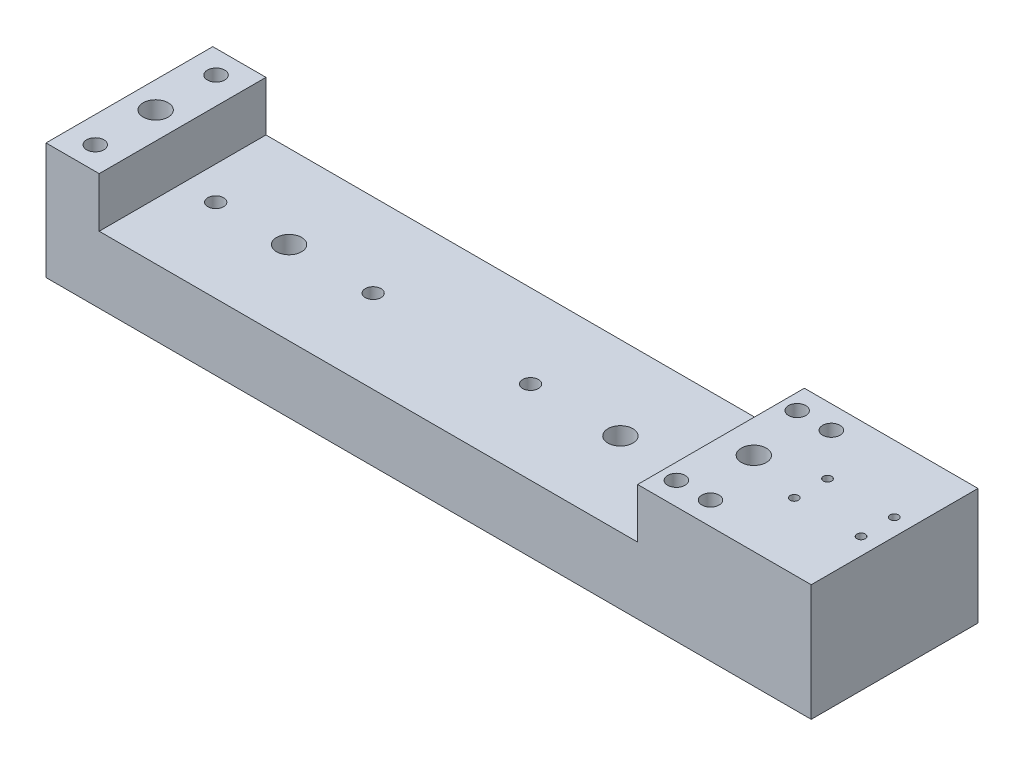
SolidWorks part; units mm, degrees
material "McMaster 6061-T6"
ref_plane "Front Plane" through (0, 0, 0) normal (0, 0, 1) x (1, 0, 0)
ref_plane "Top Plane" through (0, 0, 0) normal (0, 1, 0) x (1, 0, 0)
ref_plane "Right Plane" through (0, 0, 0) normal (1, 0, 0) x (0, 0, -1)
sketch "Sketch1" plane through (0, 0, 0) normal (0, 0, 1) x (1, 0, 0)
  line L0 (-125.125, 0) -> (-125.125, -6.35)
  line L1 (-125.125, -6.35) -> (166.225, -6.35)
  line L2 (166.225, -6.35) -> (166.225, 0)
  line B0 (-125.125, 38.05) -> (-104.875, 38.05)
  line B1 (-104.875, 38.05) -> (-104.875, 19.05)
  line B2 (-104.875, 19.05) -> (100.125, 19.05)
  line B3 (100.125, 19.05) -> (100.125, 38.05)
  line B4 (100.125, 38.05) -> (125.125, 38.05)
  line B5 (-125.125, 38.05) -> (-125.125, 0)
  line B6 (-125.125, 0) -> (125.125, 0)
  line B7 (125.125, 0) -> (125.125, 38.05)
  line B8 (125.125, 38.05) -> (166.225, 38.05)
  line B9 (166.225, 38.05) -> (166.225, 0)
  line B10 (166.225, 0) -> (125.125, 0)
  dimension "D1" = 25.4
sketch_block_instance "Block-MainBlock Sideview-1"
sketch_block "Block-MainBlock Sideview" parameters "D1"=19.05, "D2"=38.05
extrude "Main Extrude" add sketch "Sketch1" along normal blind 63.5 contours B6 B7 B4 B3 B2 B1 B0 B5 | B10 B9 B8 B7 | B6 L0 L1 L2
sketch "Sketch3" plane through (0, 38.05, 0) normal (0, 1, 0) x (1, 0, 0)
  line L0 (166.225, -63.5) -> (166.225, 0) construction
  line L1 (125.125, -31.75) -> (166.225, -31.75) construction
  line L2 (166.225, -63.5) -> (166.225, 0) construction
  point P4 (166.225, -31.75)
  line B0 (-105.125, -1.75) -> (-105.125, -61.75)
  line B1 (-105.125, -1.75) -> (-125.125, -1.75)
  line B2 (-125.125, -1.75) -> (-125.125, -61.75)
  line B3 (-105.125, -61.75) -> (-125.125, -61.75)
  line B4 (125.125, -1.75) -> (125.125, -61.75)
  line B5 (125.125, -1.75) -> (100.125, -1.75)
  line B6 (100.125, -1.75) -> (100.125, -61.75)
  line B7 (125.125, -61.75) -> (100.125, -61.75)
  circle B8 centre (-115.125, -54.75) radius 3.3
  circle B9 centre (119.125, -8.75) radius 3.3
  circle B10 centre (106.125, -8.75) radius 3.3
  circle B11 centre (119.125, -54.75) radius 3.3
  circle B12 centre (106.125, -54.75) radius 3.3
  circle B13 centre (-115.125, -8.75) radius 3.3
sketch_block_instance "Block-MainBlock Topview-1"
sketch_block "Block-MainBlock Topview"
extrude "Rail Block Mounting Holes" cut sketch "Sketch3" against normal blind 6.35 contours B12 | B11 | B10 | B9 | B8 | B13
sketch "Sketch4" plane through (0, 38.05, 0) normal (0, 1, 0) x (1, 0, 0)
  line L1 (166.225, -63.5) -> (166.225, 0) construction
  point P1 (166.225, -31.75)
  point P4 (166.225, -31.75)
  line B0 (128.0229, -22.2586) -> (166.1229, -22.25) construction
  line B1 (166.2182, -1.75) -> (100.1182, -1.7649)
  line B2 (100.1182, -1.7649) -> (100.1318, -61.7649)
  line B3 (100.1318, -61.7649) -> (166.2318, -61.75)
  line B4 (166.2318, -61.75) -> (166.2182, -1.75)
  line B5 (128.0229, -22.2586) -> (128.0271, -41.2586) construction
  line B6 (128.0271, -41.2586) -> (166.1271, -41.25) construction
  circle B7 centre (159.7736, -25.4265) radius 1.5875
  circle B8 centre (134.3764, -38.0822) radius 1.5875
  circle B9 centre (159.7764, -38.0765) radius 1.5875
  circle B10 centre (134.3736, -25.4322) radius 1.5875
sketch_block_instance "Block-MotorMounting TopView-1"
sketch_block "Block-MotorMounting TopView"
extrude "Motor Mounting Holes" cut sketch "Sketch4" against normal blind 6.35 contours B10 | B7 | B9 | B8
sketch "Sketch8" plane through (0, 19.05, 0) normal (0, 1, 0) x (1, 0, 0)
  line L0 (166.225, -63.5) -> (166.225, 0) construction
  point P2 (166.225, -31.75)
  point P3 (-59.7666, -31.75)
  point P4 (100.125, -31.75)
  point P5 (33.781, 81.3153)
  point P6 (0, 0)
  line B0 (27.625, -31.75) -> (87.625, -31.75)
  line B1 (-104.875, -25.6562) -> (-104.875, -37.8438)
  line B2 (-104.875, -37.8438) -> (100.125, -37.8438)
  line B3 (100.125, -37.8438) -> (100.125, -25.6562)
  line B4 (100.125, -25.6562) -> (-104.875, -25.6562)
  line B5 (100.125, 0.175) -> (-104.875, 0.175)
  line B6 (-104.875, 0.175) -> (-104.875, -63.325)
  line B7 (-104.875, -63.325) -> (100.125, -63.325)
  line B8 (100.125, -63.325) -> (100.125, 0.175)
  arc B9 (27.625, -34.75) -> (27.625, -28.75) centre (27.625, -31.75) ccw
  arc B10 (27.625, -28.75) -> (27.625, -34.75) centre (27.625, -31.75) ccw
  arc B11 (87.625, -34.75) -> (87.625, -28.75) centre (87.625, -31.75) ccw
  arc B12 (87.625, -28.75) -> (87.625, -34.75) centre (87.625, -31.75) ccw
  arc B13 (-32.319, -34.75) -> (-32.319, -28.75) centre (-32.319, -31.75) ccw
  arc B14 (-32.319, -28.75) -> (-32.319, -34.75) centre (-32.319, -31.75) ccw
  arc B15 (-92.263, -34.75) -> (-92.263, -28.75) centre (-92.263, -31.75) ccw
  arc B16 (-92.263, -28.75) -> (-92.263, -34.75) centre (-92.263, -31.75) ccw
sketch_block_instance "Block-CarriageMounting-1"
sketch_block "Block-CarriageMounting" parameters "D1"=60
extrude "Rail Mounting Holes" cut sketch "Sketch8" against normal blind 6.35
sketch "Sketch5" plane through (0, 0, 0) normal (0, 1, 0) x (1, 0, 0)
  line L0 (61.825, -31.75) -> (112.625, -31.75) construction
  line L1 (-125.125, -63.5) -> (-125.125, 0) construction
  line L2 (-115.125, -31.75) -> (-64.325, -31.75) construction
  line L3 (-115.125, -31.75) -> (-115.125, -54.75) construction
  line L4 (-104.875, -63.5) -> (100.125, -63.5) construction
  line L5 (106.125, -8.75) -> (119.125, -54.75) construction
  circle A0 centre (-115.125, -31.75) radius 3.3122
  circle A1 centre (-64.325, -31.75) radius 3.3122
  circle A2 centre (61.825, -31.75) radius 3.3122
  circle A3 centre (112.625, -31.75) radius 3.3122
  point P1 (112.625, -31.75)
  point P11 (-125.125, -31.75)
  dimension "D1" = 6.6243
  dimension "D2" = 50.8
extrude "Cut-Extrude3" cut sketch "Sketch5" along normal through all both and the other way through all
ref_plane "Plane1" through (0, 6.35, 0) normal (0, -1, 0) x (-1, 0, 0)
sketch "Sketch7" plane through (0, 6.35, 0) normal (0, -1, 0) x (-1, 0, 0)
  circle A12 centre (-61.825, -31.75) radius 3.3122 construction
  circle A13 centre (-112.625, -31.75) radius 3.3122 construction
  circle A14 centre (64.325, -31.75) radius 3.3122 construction
  circle A15 centre (115.125, -31.75) radius 3.3122 construction
  circle A16 centre (-61.825, -31.75) radius 3.3122 construction
  circle A17 centre (-112.625, -31.75) radius 3.3122 construction
  circle A18 centre (64.325, -31.75) radius 3.3122 construction
  circle A19 centre (115.125, -31.75) radius 3.3122 construction
  circle A20 centre (115.125, -31.75) radius 4.7625
  circle A21 centre (64.325, -31.75) radius 4.7625
  circle A22 centre (-112.625, -31.75) radius 4.7625
  circle A23 centre (-61.825, -31.75) radius 4.7625
  dimension "D1" = 9.525
extrude "Cut-Extrude6" cut sketch "Sketch7" against normal through all
fillet "Fillet2" [suppressed] radius 2.54
sketch "Split Sketch" plane through (0, -6.35, 0) normal (0, -1, 0) x (1, 0, 0)
  line L0 (-125.125, 0) -> (166.225, 0) construction
  line L1 (166.225, 63.5) -> (166.225, 0) construction
  line B0 (-125.125, 0) -> (166.225, 0) construction
  line B1 (166.225, 0) -> (166.225, 63.5) construction
  line B2 (144.375, 0) -> (144.375, 63.5)
  line B3 (144.375, 63.5) -> (30.075, 63.5)
  line B4 (30.075, 63.5) -> (30.075, 0)
  line B5 (30.075, 0) -> (144.375, 0)
  line B6 (-146.875, 63.5) -> (-146.875, 0)
  line B7 (-32.575, 0) -> (-32.575, 63.5)
  line B8 (-32.575, 63.5) -> (-146.875, 63.5)
sketch_block_instance "Block-Electromagnet Imprint-1"
sketch_block "Block1"
ref_plane "Plane3" through (-32.575, 0, 0) normal (1, 0, 0) x (0, 0, -1)
ref_plane "Plane4" through (30.075, 0, 0) normal (1, 0, 0) x (0, 0, -1)
ref_plane "Plane5" through (144.375, 0, 0) normal (1, 0, 0) x (0, 0, -1)
split line "Split Line2"
